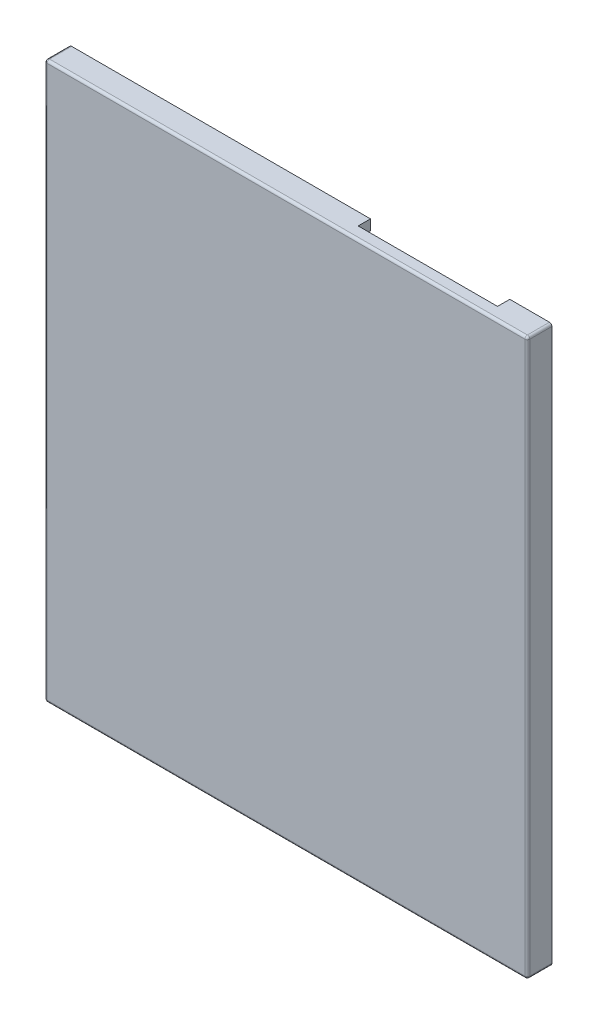
SolidWorks part; units mm, degrees
ref_plane "前视基准面" through (0, 0, 0) normal (0, 0, 1) x (1, 0, 0)
ref_plane "上视基准面" through (0, 0, 0) normal (0, 1, 0) x (1, 0, 0)
ref_plane "右视基准面" through (0, 0, 0) normal (1, 0, 0) x (0, 0, -1)
sketch "草图1" plane through (0, 0, 0) normal (0, 0, 1) x (1, 0, 0)
  line L1 (-28.25, 32.75) -> (28.25, 32.75)
  line L2 (-28.25, 32.75) -> (-28.25, -32.75)
  line L3 (-28.25, -32.75) -> (28.25, -32.75)
  line L4 (28.25, 32.75) -> (28.25, -32.75)
  line L5 (-28.25, 32.75) -> (28.25, -32.75) construction
  line L6 (-28.25, -32.75) -> (28.25, 32.75) construction
  point P0 (0, 0)
  dimension "D1" = 56.5
  dimension "D2" = 65.5
extrude "凸台-拉伸1" add sketch "草图1" along normal blind 1.5
sketch "草图2" plane through (0, 0, 1.5) normal (0, 0, 1) x (1, 0, 0)
  line L1 (-29.5, 34) -> (29.5, 34)
  line L2 (-29.5, 34) -> (-29.5, -34)
  line L3 (-29.5, -34) -> (29.5, -34)
  line L4 (29.5, 34) -> (29.5, -34)
  line L5 (-29.5, 34) -> (29.5, -34) construction
  line L6 (-29.5, -34) -> (29.5, 34) construction
  line L7 (-28.25, 32.75) -> (28.25, 32.75)
  line L8 (-28.25, 32.75) -> (-28.25, -32.75)
  line L9 (-28.25, -32.75) -> (28.25, -32.75)
  line L10 (28.25, 32.75) -> (28.25, -32.75)
  line L11 (-28.25, 32.75) -> (28.25, -32.75) construction
  line L12 (-28.25, -32.75) -> (28.25, 32.75) construction
  point P0 (0, 0)
  point P6 (0, 0)
  dimension "D1" = 59
  dimension "D2" = 68
extrude "凸台-拉伸2" add sketch "草图2" against normal blind 3
fillet "圆角1" radius 0.3 8 edges at (0, -34, 1.5) (-29.5, 0, 1.5) (0, 34, 1.5) (29.5, 0, 1.5) (-29.5, 34, 0) (-29.5, -34, 0) (29.5, -34, 0) (29.5, 34, 0)
sketch "草图3" plane through (0, 0, 0) normal (0, 0, -1) x (-1, 0, 0)
  line L0 (-27.9295, -32.2213) -> (-27.9295, 32.2786)
  line L1 (2.2014, -32.1214) -> (27.6018, -32.1214)
  line L2 (-27.8976, 32.379) -> (27.6018, 32.379)
  line L3 (-16.8736, -32.1214) -> (-27.9295, -32.1214)
  line L4 (-16.8736, -32.1214) -> (-14.6155, -32.1214)
  line L5 (-14.6155, -32.1214) -> (-14.6155, -30.887)
  line L6 (-14.6155, -30.887) -> (-4.7044, -30.887)
  line L7 (-4.7044, -30.887) -> (-4.7044, -32.1214)
  line L8 (-4.7044, -32.1214) -> (0.2765, -32.1214)
  line L9 (0.2765, -32.1214) -> (2.2014, -32.1214)
  line L10 (27.6018, -32.129) -> (27.6018, 32.3794)
  line L11 (0.6049, 9.1324) -> (-0.4459, 9.1324)
  line L12 (-0.4459, 9.1324) -> (0.6049, 9.1324)
  line L13 (0.6049, 8.3968) -> (-0.4459, 8.3968)
  line L14 (-0.4459, 8.3968) -> (0.6049, 8.3968)
  line L15 (-3.3951, 9.1324) -> (-4.4459, 9.1324)
  line L16 (-4.4459, 9.1324) -> (-3.3951, 9.1324)
  line L17 (-3.3951, 8.3968) -> (-4.4459, 8.3968)
  line L18 (-4.4459, 8.3968) -> (-3.3951, 8.3968)
  line L19 (0.6049, 5.2724) -> (-0.4459, 5.2724)
  line L20 (-0.4459, 5.2724) -> (0.6049, 5.2724)
  line L21 (0.6049, 4.5368) -> (-0.4459, 4.5368)
  line L22 (-0.4459, 4.5368) -> (0.6049, 4.5368)
  line L23 (-3.3951, 5.2724) -> (-4.4459, 5.2724)
  line L24 (-4.4459, 5.2724) -> (-3.3951, 5.2724)
  line L25 (-3.3951, 4.5368) -> (-4.4459, 4.5368)
  line L26 (-4.4459, 4.5368) -> (-3.3951, 4.5368)
  circle A0 centre (17.7304, -21.5866) radius 1.2693
  circle A1 centre (17.7306, -21.5865) radius 1.6754
  circle A2 centre (4.5904, -21.5866) radius 1.2693
  circle A3 centre (4.5904, -21.5865) radius 1.6754
  circle A4 centre (7.6604, -24.0366) radius 0.4906
  circle A5 centre (7.6605, -24.0366) radius 0.8004
  circle A6 centre (10.1603, -24.0366) radius 0.4906
  circle A7 centre (10.1604, -24.0366) radius 0.8004
  circle A8 centre (12.1603, -24.0366) radius 0.4906
  circle A9 centre (12.1604, -24.0366) radius 0.8004
  circle A10 centre (-20.5546, 32.3386) radius 0.5906
  circle A11 centre (-20.5546, 32.3387) radius 0.7874
  circle A12 centre (-18.6054, 32.3393) radius 0.5906
  circle A13 centre (-18.6054, 32.3395) radius 0.7874
  circle A14 centre (-16.6054, 32.3393) radius 0.5906
  circle A15 centre (-16.6054, 32.3395) radius 0.7874
  circle A16 centre (-14.5545, 32.3385) radius 0.5906
  circle A17 centre (-14.5546, 32.3387) radius 0.7874
  circle A18 centre (8.4227, 13.4437) radius 0.5404
  circle A19 centre (8.4228, 13.4437) radius 0.875
  circle A20 centre (5.9226, 13.4437) radius 0.5404
  circle A21 centre (5.9227, 13.4437) radius 0.875
  circle A22 centre (1.3295, 6.1346) radius 0.2413
  circle A23 centre (1.3296, 6.1346) radius 0.3754
  circle A24 centre (0.3795, 6.1346) radius 0.2413
  circle A25 centre (0.3796, 6.1346) radius 0.3754
  circle A26 centre (-0.5707, 6.1346) radius 0.2413
  circle A27 centre (-0.5706, 6.1346) radius 0.3754
  circle A28 centre (-1.4706, 6.1346) radius 0.2413
  circle A29 centre (-1.4705, 6.1346) radius 0.3754
  circle A30 centre (-2.3706, 6.1346) radius 0.2413
  circle A31 centre (-2.3704, 6.1346) radius 0.3754
  circle A32 centre (-4.2207, 6.1346) radius 0.2413
  circle A33 centre (-4.2206, 6.1346) radius 0.3754
  circle A34 centre (-5.1707, 6.1346) radius 0.2413
  circle A35 centre (-5.1705, 6.1346) radius 0.3754
  circle A36 centre (-5.1707, 7.5346) radius 0.2413
  circle A37 centre (-5.1705, 7.5346) radius 0.3754
  circle A38 centre (-3.2707, 7.5346) radius 0.2413
  circle A39 centre (-3.2706, 7.5346) radius 0.3754
  circle A40 centre (-2.3706, 7.5346) radius 0.2413
  circle A41 centre (-2.3704, 7.5346) radius 0.3754
  circle A42 centre (-1.4706, 7.5346) radius 0.2413
  circle A43 centre (-1.4705, 7.5346) radius 0.3754
  circle A44 centre (0.3795, 7.5346) radius 0.2413
  circle A45 centre (0.3796, 7.5346) radius 0.3754
  circle A46 centre (1.3295, 7.5346) radius 0.2413
  circle A47 centre (1.3296, 7.5346) radius 0.3754
  circle A48 centre (-4.2207, 7.5346) radius 0.2413
  circle A49 centre (-4.2206, 7.5346) radius 0.3754
  circle A50 centre (12.1552, 3.3058) radius 0.4906
  circle A51 centre (12.1553, 3.3058) radius 0.8004
  circle A52 centre (10.1552, 3.3058) radius 0.4906
  circle A53 centre (10.1553, 3.3058) radius 0.8004
  circle A54 centre (7.6553, 3.3058) radius 0.4906
  circle A55 centre (7.6554, 3.3058) radius 0.8004
  circle A56 centre (4.5853, 5.7558) radius 1.2693
  circle A57 centre (4.5853, 5.7559) radius 1.6754
  circle A58 centre (17.7253, 5.7557) radius 1.2693
  circle A59 centre (17.7255, 5.7559) radius 1.6754
  circle A60 centre (12.2212, -5.8255) radius 0.4906
  circle A61 centre (12.2214, -5.8255) radius 0.8004
  circle A62 centre (10.2212, -5.8255) radius 0.4906
  circle A63 centre (10.2214, -5.8255) radius 0.8004
  circle A64 centre (7.7214, -5.8255) radius 0.4906
  circle A65 centre (7.7215, -5.8255) radius 0.8004
  circle A66 centre (4.6514, -3.3755) radius 1.2693
  circle A67 centre (4.6514, -3.3754) radius 1.6754
  circle A68 centre (17.7913, -3.3756) radius 1.2693
  circle A69 centre (17.7916, -3.3754) radius 1.6754
  circle A70 centre (12.3482, -14.9568) radius 0.4906
  circle A71 centre (12.3484, -14.9568) radius 0.8004
  circle A72 centre (10.3482, -14.9568) radius 0.4906
  circle A73 centre (10.3484, -14.9568) radius 0.8004
  circle A74 centre (7.8484, -14.9568) radius 0.4906
  circle A75 centre (7.8485, -14.9568) radius 0.8004
  circle A76 centre (4.7784, -12.5068) radius 1.2693
  circle A77 centre (4.7784, -12.5067) radius 1.6754
  circle A78 centre (17.9183, -12.5069) radius 1.2693
  circle A79 centre (17.9186, -12.5067) radius 1.6754
  circle A80 centre (16.571, 13.3979) radius 0.5404
  circle A81 centre (16.5711, 13.3979) radius 0.875
  circle A82 centre (14.071, 13.3979) radius 0.5404
  circle A83 centre (14.071, 13.3979) radius 0.875
  circle A84 centre (0.2693, 13.4106) radius 0.5404
  circle A85 centre (0.2694, 13.4106) radius 0.875
  circle A86 centre (-2.2308, 13.4106) radius 0.5404
  circle A87 centre (-2.2307, 13.4106) radius 0.875
  circle A88 centre (7.3723, -28.7889) radius 0.5404
  circle A89 centre (7.3722, -28.7889) radius 0.875
  circle A90 centre (9.8723, -28.7889) radius 0.5404
  circle A91 centre (9.8724, -28.7889) radius 0.875
  circle A92 centre (12.3723, -28.7889) radius 0.5404
  circle A93 centre (12.3722, -28.7889) radius 0.875
  circle A94 centre (14.8723, -28.7889) radius 0.5404
  circle A95 centre (14.8723, -28.7889) radius 0.875
  circle A96 centre (14.6604, -24.0366) radius 0.4906
  circle A97 centre (-20.5546, 30.5607) radius 0.1585
  circle A98 centre (-18.5785, 30.52) radius 0.1585
  circle A99 centre (-14.5399, 30.6521) radius 0.1585
  circle A100 centre (-16.6024, 30.5988) radius 0.1585
  arc A101 (0.6049, 9.1324) -> (0.6049, 8.3968) centre (0.6049, 8.7646) ccw
  arc A102 (-0.4459, 8.3968) -> (-0.4459, 9.1324) centre (-0.4459, 8.7646) ccw
  arc A103 (-3.3951, 9.1324) -> (-3.3951, 8.3968) centre (-3.3951, 8.7646) ccw
  arc A104 (-4.4459, 8.3968) -> (-4.4459, 9.1324) centre (-4.4459, 8.7646) ccw
  arc A105 (0.6049, 5.2724) -> (0.6049, 4.5368) centre (0.6049, 4.9046) ccw
  arc A106 (-0.4459, 4.5368) -> (-0.4459, 5.2724) centre (-0.4459, 4.9046) ccw
  arc A107 (-3.3951, 5.2724) -> (-3.3951, 4.5368) centre (-3.3951, 4.9046) ccw
  arc A108 (-4.4459, 4.5368) -> (-4.4459, 5.2724) centre (-4.4459, 4.9046) ccw
  circle A109 centre (14.6553, 3.3058) radius 0.4906
  circle A110 centre (14.7213, -5.8255) radius 0.4906
  circle A111 centre (14.8483, -14.9568) radius 0.4906
  point P0 (0, 0)
sketch "草图4" plane through (0, 0, 0) normal (0, 0, -1) x (-1, 0, 0)
  line L0 (28.25, 32.75) -> (28.25, -32.75) construction
  line L1 (-4.75, 16.25) -> (20.25, 16.25)
  line L2 (-4.75, 16.25) -> (-4.75, 11.25)
  line L3 (-4.75, 11.25) -> (20.25, 11.25)
  line L4 (20.25, 16.25) -> (20.25, 11.25)
  line L5 (-9.4494, 9.75) -> (21.25, 9.75)
  line L6 (-9.4494, 9.75) -> (-9.4494, 1.25)
  line L7 (-9.4494, 1.25) -> (21.25, 1.25)
  line L8 (21.25, 9.75) -> (21.25, 1.25)
  line L9 (1.25, -0.75) -> (21.25, -0.75)
  line L10 (1.25, -0.75) -> (1.25, -30.75)
  line L11 (1.25, -30.75) -> (21.25, -30.75)
  line L12 (21.25, -0.75) -> (21.25, -30.75)
  line L13 (28.25, -32.75) -> (-28.25, -32.75) construction
  line L14 (28.25, 32.75) -> (28.25, -32.75) construction
  dimension "D1" = 30
  dimension "D2" = 20
  dimension "D3" = 7
  dimension "D4" = 2
  dimension "D5" = 7
  dimension "D6" = 8.5
  dimension "D7" = 2
  dimension "D8" = 25
  dimension "D9" = 1.5
  dimension "D10" = 8
  dimension "D11" = 5
extrude "切除-拉伸1" cut sketch "草图4" against normal blind 1
sketch "草图5" plane through (0, 0, -1.5) normal (0, 0, -1) x (-1, 0, 0)
  line L0 (-28.25, 32.75) -> (28.25, 32.75) construction
  line L1 (-24.3537, 32.75) -> (-7.3187, 32.75)
  line L2 (-24.3537, 32.75) -> (-24.3537, 34)
  line L3 (-24.3537, 34) -> (-7.3187, 34)
  line L4 (-7.3187, 32.75) -> (-7.3187, 34)
  line L5 (-29.2, 34) -> (29.2, 34) construction
extrude "切除-拉伸2" cut sketch "草图5" against normal blind 1.5
